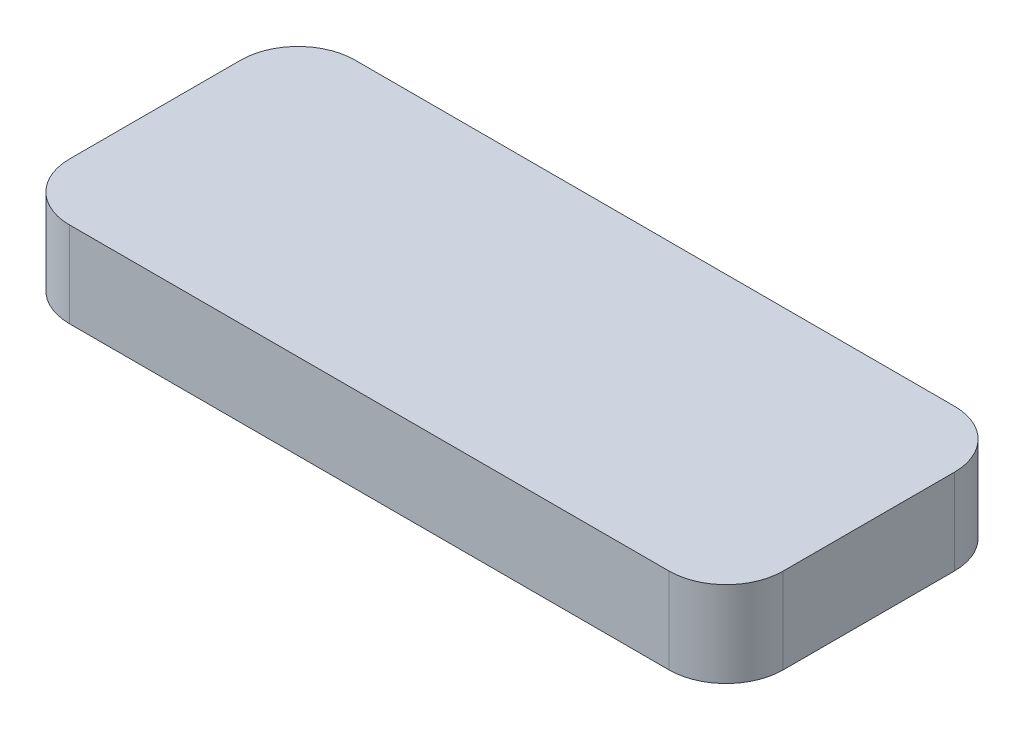
SolidWorks part; units mm, degrees
ref_plane "Front Plane" through (0, 0, 0) normal (0, 0, 1) x (1, 0, 0)
ref_plane "Top Plane" through (0, 0, 0) normal (0, 1, 0) x (1, 0, 0)
ref_plane "Right Plane" through (0, 0, 0) normal (1, 0, 0) x (0, 0, -1)
sketch "Sketch1" plane through (0, 0, 0) normal (0, 1, 0) x (1, 0, 0)
  line L1 (12.5, -5) -> (-12.5, -5)
  line L2 (12.5, -5) -> (12.5, 5)
  line L3 (12.5, 5) -> (-12.5, 5)
  line L4 (-12.5, -5) -> (-12.5, 5)
  line L5 (12.5, -5) -> (-12.5, 5) construction
  line L6 (12.5, 5) -> (-12.5, -5) construction
  point P0 (0, 0)
  dimension "D1" = 25
  dimension "D2" = 10
extrude "Boss-Extrude1" add sketch "Sketch1" along normal blind 3
fillet "Fillet1" radius 2 4 edges at (-12.5, 1.5, -5) (12.5, 1.5, -5) (-12.5, 1.5, 5) (12.5, 1.5, 5)
